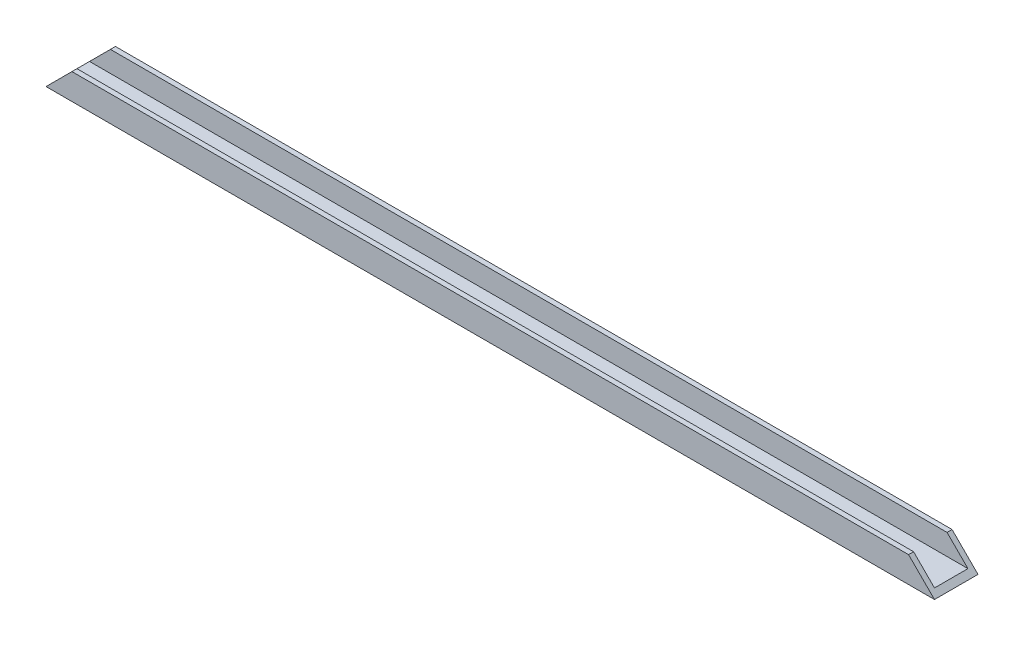
SolidWorks part; units mm, degrees
ref_plane "Front Plane" through (0, 0, 0) normal (0, 0, 1) x (1, 0, 0)
ref_plane "Top Plane" through (0, 0, 0) normal (0, 1, 0) x (1, 0, 0)
ref_plane "Right Plane" through (0, 0, 0) normal (1, 0, 0) x (0, 0, -1)
sketch "Sketch1" plane through (0, 0, 0) normal (1, 0, 0) x (0, 0, -1)
  line L0 (-4, 5) -> (-4, 0)
  line L1 (-4, 0) -> (4, 0)
  line L2 (4, 0) -> (4, 5)
  line L3 (-5.2, 5) -> (-5.2, -1.2)
  line L4 (-5.2, -1.2) -> (5.2, -1.2)
  line L5 (5.2, -1.2) -> (5.2, 5)
  line L6 (-5.2, 5) -> (-4, 5)
  line L7 (4, 5) -> (5.2, 5)
  point P2 (0, 0)
  dimension "D1" = 5
  dimension "D2" = 5
  dimension "D3" = 8
  dimension "D4" = 1.2
  dimension "D5" = 1.2
  dimension "D6" = 1.2
extrude "Boss-Extrude1" add sketch "Sketch1" along normal mid plane 212.4
sketch "Sketch3" plane through (0, 0, 5.2) normal (0, 0, 1) x (1, 0, 0)
  line L0 (-106.2, 5) -> (-106.2, -1.2)
  line L1 (-106.2, -1.2) -> (-100, 5)
  line L2 (106.2, 5) -> (-106.2, 5) construction
  line L3 (-100, 5) -> (-106.2, 5)
  line L4 (0, 32.8147) -> (0, -57.253) construction
  line L5 (106.2, 5) -> (106.2, -1.2)
  line L6 (100, 5) -> (106.2, 5)
  line L7 (106.2, -1.2) -> (100, 5)
  dimension "D1" = 45
extrude "Cut-Extrude1" cut sketch "Sketch3" against normal through all
